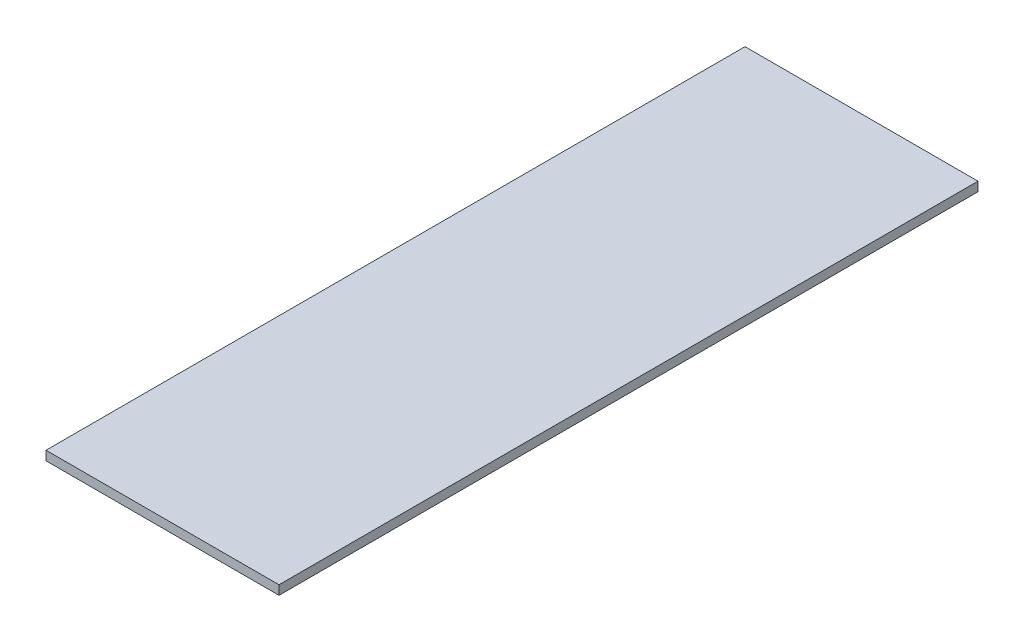
SolidWorks part; units mm, degrees
ref_plane "Front Plane" through (0, 0, 0) normal (0, 0, 1) x (1, 0, 0)
ref_plane "Top Plane" through (0, 0, 0) normal (0, 1, 0) x (1, 0, 0)
ref_plane "Right Plane" through (0, 0, 0) normal (1, 0, 0) x (0, 0, -1)
sketch "Sketch1" plane through (0, 0, 0) normal (0, 1, 0) x (1, 0, 0)
  line L1 (0, 0) -> (25.4, 0)
  line L2 (0, 0) -> (0, 76.2)
  line L3 (0, 76.2) -> (25.4, 76.2)
  line L4 (25.4, 0) -> (25.4, 76.2)
  dimension "D1" = 25.4
  dimension "D2" = 76.2
extrude "Boss-Extrude1" add sketch "Sketch1" along normal blind 1
